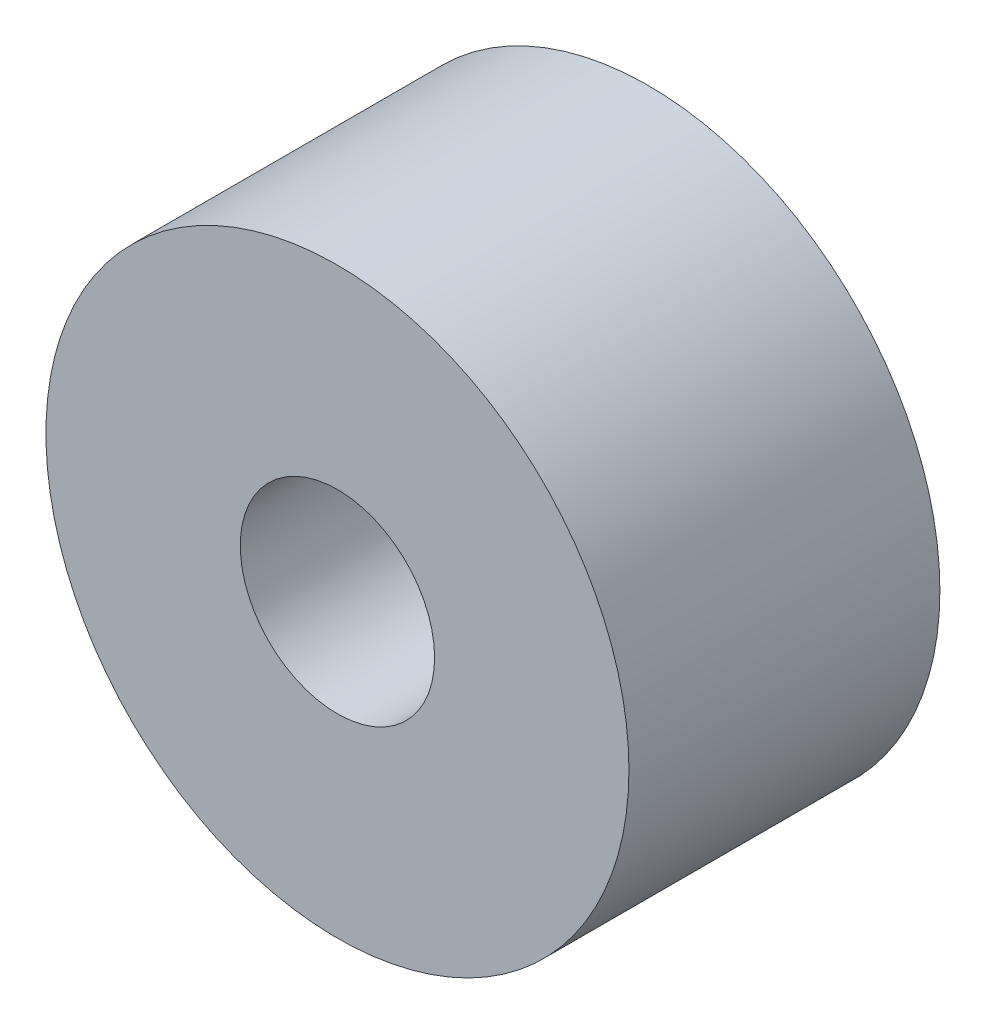
SolidWorks part; units mm, degrees
ref_plane "Front Plane" through (0, 0, 0) normal (0, 0, 1) x (1, 0, 0)
ref_plane "Top Plane" through (0, 0, 0) normal (0, 1, 0) x (1, 0, 0)
ref_plane "Right Plane" through (0, 0, 0) normal (1, 0, 0) x (0, 0, -1)
sketch "Sketch1" plane through (0, 0, 0) normal (0, 0, 1) x (1, 0, 0)
  circle A0 centre (0, 0) radius 15
  dimension "D1" = 30
extrude "Boss-Extrude1" add sketch "Sketch1" along normal blind 16
sketch "Sketch2" plane through (0, 0, 16) normal (0, 0, 1) x (1, 0, 0)
  circle A0 centre (0, 0) radius 5
  dimension "D1" = 10
extrude "Cut-Extrude1" cut sketch "Sketch2" against normal blind 16
